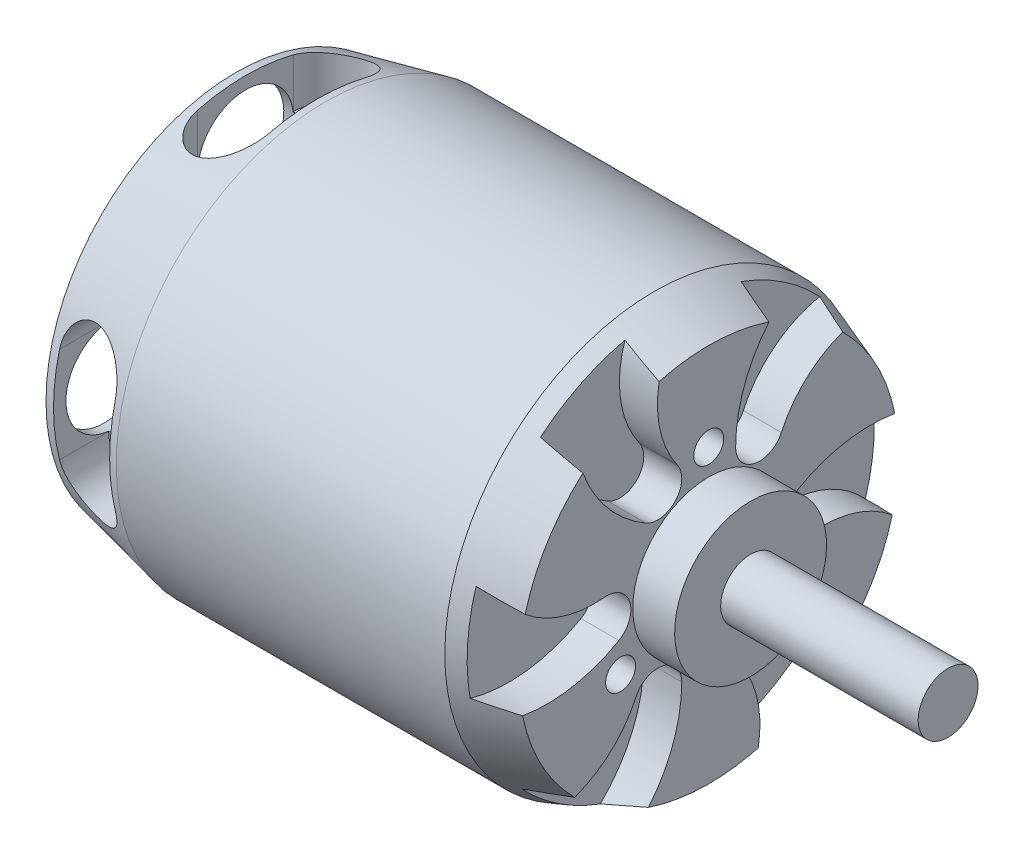
SolidWorks part; units mm, degrees
ref_plane "Front Plane" through (0, 0, 0) normal (0, 0, 1) x (1, 0, 0)
ref_plane "Top Plane" through (0, 0, 0) normal (0, 1, 0) x (1, 0, 0)
ref_plane "Right Plane" through (0, 0, 0) normal (1, 0, 0) x (0, 0, -1)
sketch "Sketch1" plane through (0, 0, 0) normal (0, 0, 1) x (1, 0, 0)
  line L0 (0, 0) -> (0, 15.866)
  line L1 (0, 15.866) -> (7.5, 17.5)
  line L2 (7.5, 17.5) -> (34.9512, 17.5)
  line L3 (34.9512, 17.5) -> (39.5, 15.866)
  line L4 (39.5, 15.866) -> (39.5, 6.3467)
  line L5 (39.5, 6.3467) -> (43, 6.3467)
  line L6 (43, 6.3467) -> (43, 2.5)
  line L7 (43, 2.5) -> (59.5, 2.5)
  line L8 (59.5, 2.5) -> (59.5, 0)
  line L9 (59.5, 0) -> (0, 0) construction
  line L10 (0, 0) -> (59.5, 0)
  dimension "D1" = 5
  dimension "D2" = 35
  dimension "D3" = 16.5
  dimension "D4" = 3.5
  dimension "D5" = 59.5
  dimension "D6" = 32
revolve "Revolve1" add sketch "Sketch1" angle 360 about L9
sketch "Sketch2" plane through (39.5, 0, 0) normal (1, 0, 0) x (0, 0, -1)
  circle A0 centre (0, 8.5) radius 1.25
  circle A1 centre (7.3612, -4.25) radius 1.25
  circle A2 centre (-7.3612, -4.25) radius 1.25
  dimension "D1" = 2.5
  dimension "D2" = 8.5
  dimension "D3" = 3
extrude "Cut-Extrude1" cut sketch "Sketch2" against normal blind 6.35
sketch "Sketch3" plane through (0, 0, 0) normal (-1, 0, 0) x (0, 0, 1)
  line L0 (-6.7175, -6.7175) -> (6.7175, 6.7175) construction
  line L1 (0, 0) -> (6.9035, 0) construction
  line L2 (-8.8388, 8.8388) -> (8.8388, -8.8388) construction
  circle A0 centre (-8.8388, 8.8388) radius 1.5
  circle A1 centre (8.8388, -8.8388) radius 1.5
  circle A2 centre (6.7175, 6.7175) radius 1.5
  circle A3 centre (-6.7175, -6.7175) radius 1.5
  dimension "D1" = 25
  dimension "D3" = 19
  dimension "D4" = 9.5
  dimension "D5" = 3
  dimension "D2" = 12.5
  dimension "D6" = 45
  dimension "D7" = 45
extrude "Cut-Extrude2" cut sketch "Sketch3" against normal blind 6.35
sketch "Sketch6" plane through (0, 0, 0) normal (0, 1, 0) x (1, 0, 0)
  line L0 (3.8, 4) -> (3.8, -4) construction
  line L1 (6.8, 4) -> (6.8, -4)
  line L2 (0.8, 4) -> (0.8, -4)
  line L3 (0, 15.866) -> (0, -15.866) construction
  arc A0 (6.8, 4) -> (0.8, 4) centre (3.8, 4) ccw
  arc A1 (0.8, -4) -> (6.8, -4) centre (3.8, -4) ccw
  point P2 (3.8, 0)
  dimension "D1" = 3
  dimension "D2" = 3.8
  dimension "D3" = 8
extrude "Cut-Extrude5" cut sketch "Sketch6" against normal blind 6.35 from offset 17.78
sketch "Sketch4" plane through (0, 0, 0) normal (-1, 0, 0) x (0, 0, 1)
  circle A0 centre (0, 11) radius 4
  dimension "D2" = 8
  dimension "D1" = 11
extrude "Cut-Extrude3" cut sketch "Sketch4" against normal up to surface (6.8 mm away) up to face at (6.8, 14.2719, 0)
pattern_circular "CirPattern1" count 4 over 360 about axis through (0, 0, 0) along (1, 0, 0) of "Cut-Extrude3", "Cut-Extrude5"
sketch "Sketch5" plane through (39.5, 0, 0) normal (1, 0, 0) x (0, 0, -1)
  line L0 (0, 0) -> (4.25, 7.3612) construction
  line L1 (0, 0) -> (9.1318, 0) construction
  arc A0 (2.25, 7.3612) -> (6.0682, 6.528) centre (4.25, 7.3612) ccw
  arc A1 (21.996, -1.8039) -> (2.25, 7.3612) centre (14.25, 7.3612) ccw
  arc A2 (21.996, -1.8039) -> (6.0682, 6.528) centre (14.25, 2.7786) ccw
  dimension "D1" = 2
  dimension "D2" = 12
  dimension "D3" = 9
  dimension "D4" = 8.5
  dimension "D5" = 60
extrude "Cut-Extrude4" cut sketch "Sketch5" against normal blind 3.175
pattern_circular "CirPattern2" count 6 over 360 about axis through (0, 0, 0) along (1, 0, 0) of "Cut-Extrude4"
